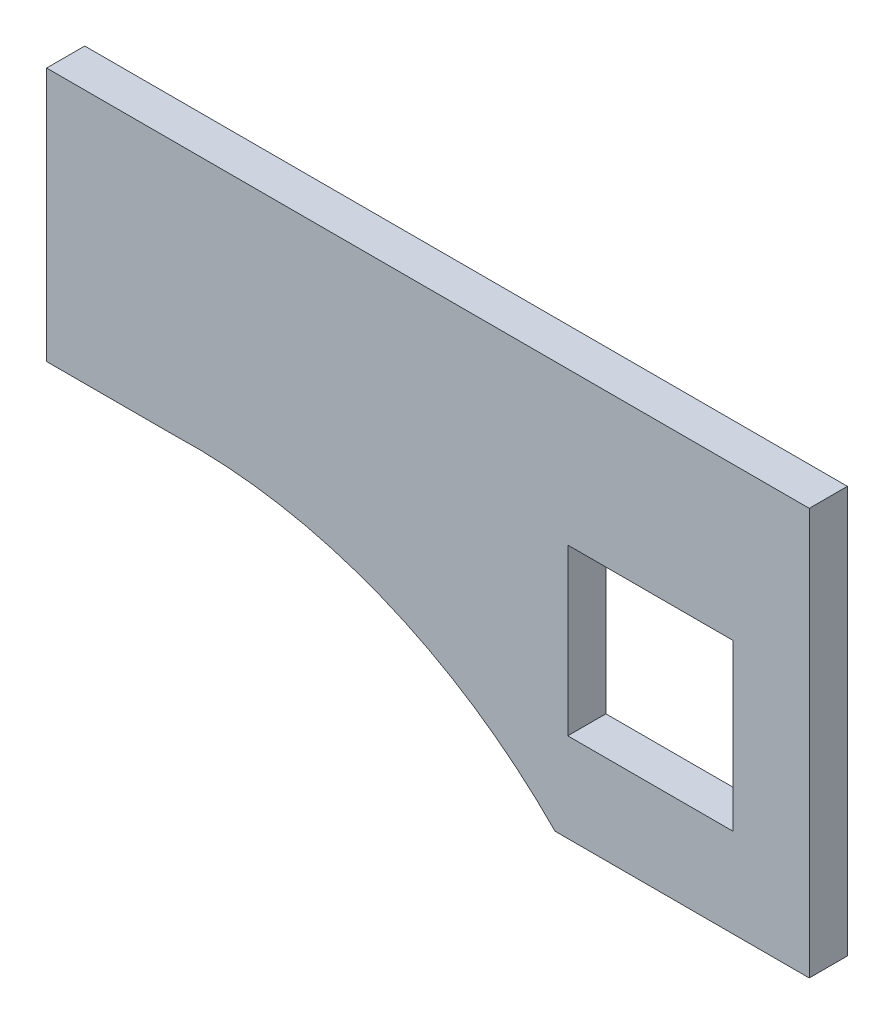
SolidWorks part; units mm, degrees
ref_plane "Front Plane" through (0, 0, 0) normal (0, 0, 1) x (1, 0, 0)
ref_plane "Top Plane" through (0, 0, 0) normal (0, 1, 0) x (1, 0, 0)
ref_plane "Right Plane" through (0, 0, 0) normal (1, 0, 0) x (0, 0, -1)
sketch "Sketch2" plane through (0, 0, 0) normal (0, 0, 1) x (1, 0, 0)
  line L9 (-7.5172, 8.1296) -> (22.4828, 8.1296)
  line L10 (22.4828, 8.1296) -> (22.4828, -7.8704)
  line L11 (22.4828, -7.8704) -> (12.4828, -7.8704)
  line L20 (-7.5172, -1.8704) -> (-2.5172, -1.8704)
  line L21 (-7.5172, 8.1296) -> (-7.5172, -1.8704)
  arc A0 (-2.5172, -1.8704) -> (12.4828, -7.8704) centre (-1.8122, -21.858) cw
  dimension "D9" = 20
  dimension "D6" = 30
  dimension "D7" = 5
  dimension "D8" = 10
  dimension "D10" = 16
extrude "Boss-Extrude1" add sketch "Sketch2" along normal blind 1.5
sketch "Sketch3" plane through (0, 0, 1.5) normal (0, 0, 1) x (1, 0, 0)
  line L5 (12.9828, 2.1296) -> (19.4828, 2.1296)
  line L6 (12.9828, 2.1296) -> (12.9828, -4.3704)
  line L7 (12.9828, -4.3704) -> (19.4828, -4.3704)
  line L8 (19.4828, 2.1296) -> (19.4828, -4.3704)
  line L9 (22.4828, -7.8704) -> (22.4828, 8.1296) construction
  line L10 (22.4828, 8.1296) -> (-7.5172, 8.1296) construction
  dimension "D1" = 6.5
  dimension "D2" = 6.5
  dimension "D3" = 3
  dimension "D4" = 6
extrude "Cut-Extrude1" cut sketch "Sketch3" against normal blind 2 contours L5 L8 L7 L6
